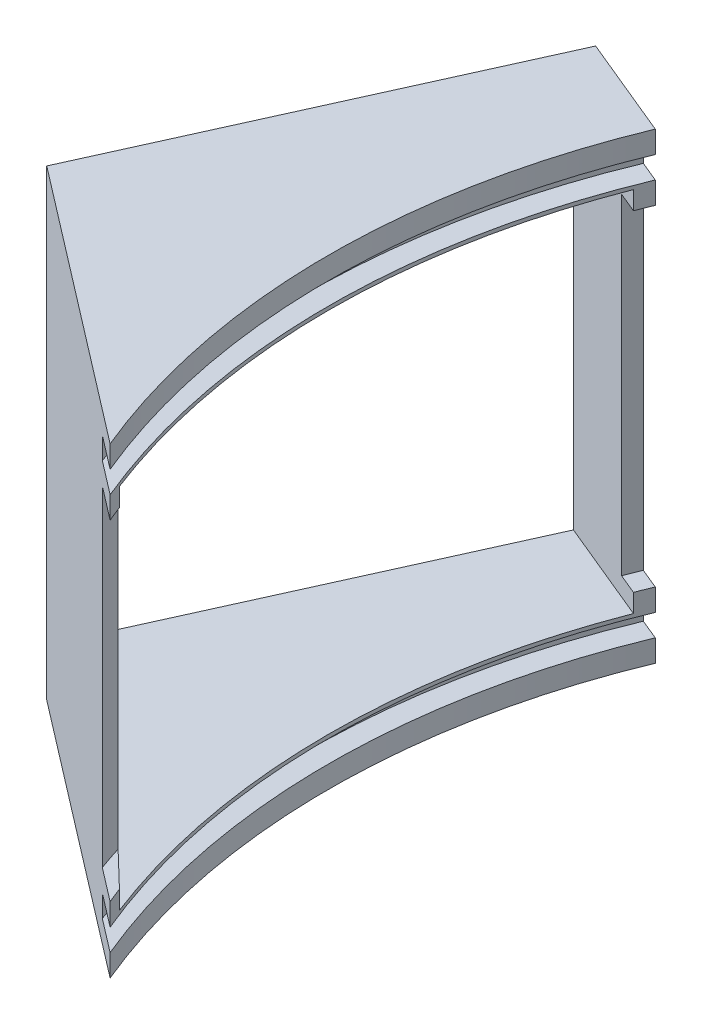
SolidWorks part; units mm, degrees
ref_plane "Front Plane" through (0, 0, 0) normal (0, 0, 1) x (1, 0, 0)
ref_plane "Top Plane" through (0, 0, 0) normal (0, 1, 0) x (1, 0, 0)
ref_plane "Right Plane" through (0, 0, 0) normal (1, 0, 0) x (0, 0, -1)
ref_axis "Axe1" through (0, 55, 0) along (0, -1, 0)
sketch "Esquisse1" plane through (0, 0, 0) normal (0, 0, 1) x (1, 0, 0)
  line L0 (-127, 31.5) -> (-97, 31.5)
  line L1 (-97, 31.5) -> (-97, 28.5)
  line L2 (-97, 28.5) -> (-100, 28.5)
  line L3 (-100, 28.5) -> (-100, 25.5)
  line L4 (-100, 25.5) -> (-97, 25.5)
  line L5 (-97, 25.5) -> (-97, 22.5)
  line L6 (-97, 22.5) -> (-100, 22.5)
  line L7 (-100, 22.5) -> (-100, -22.5)
  line L8 (-100, -22.5) -> (-97, -22.5)
  line L9 (-97, -22.5) -> (-97, -25.5)
  line L10 (-97, -25.5) -> (-100, -25.5)
  line L11 (-100, -25.5) -> (-100, -28.5)
  line L12 (-100, -28.5) -> (-97, -28.5)
  line L13 (-97, -28.5) -> (-97, -31.5)
  line L14 (-97, -31.5) -> (-127, -31.5)
  line L15 (-127, -31.5) -> (-127, 31.5)
  line L16 (0, 55) -> (0, -55) construction
  point P19 (-100, 0)
  dimension "D1" = 45
  dimension "D2" = 97
  dimension "D3" = 3
  dimension "D4" = 3
  dimension "D5" = 3
  dimension "D6" = 30
revolve "Révolution1" add sketch "Esquisse1" angle 45 mid plane about axis through (0, 55, 0) along (0, -1, 0)
sketch "Esquisse3" plane through (0, 0, 0) normal (0, 1, 0) x (1, 0, 0)
  line L0 (-127, 50.1331) -> (-90.4655, 35)
  line L1 (-90.4655, 35) -> (-90.4655, -35)
  line L2 (-90.4655, -35) -> (-127, 0.1331)
  line L3 (-127, 0.1331) -> (-127, 50.1331)
  line L4 (-89.6163, 37.1203) -> (-117.3327, 48.6008) construction
  arc A0 (-117.3327, 48.6008) -> (-117.3327, -48.6008) centre (0, 0) ccw construction
  arc A1 (-89.6163, 37.1203) -> (-89.6163, -37.1203) centre (0, 0) ccw construction
  point P7 (-93.0016, 27.5626)
  point P11 (-92.8992, -27.9058)
  point P12 (-127, 49.4988)
  dimension "D1" = 50
  dimension "D2" = 70
extrude "Enlèv. mat.-Extru.1" cut sketch "Esquisse3" against normal mid plane 50
sketch "Esquisse4" plane through (0, 31.5, 0) normal (0, 1, 0) x (1, 0, 0)
  line L0 (-117.3327, -48.6008) -> (-89.6163, -37.1203)
  line L2 (-126.7043, -8.6617) -> (-89.6163, -37.1203)
  arc A0 (-117.3327, 48.6008) -> (-117.3327, -48.6008) centre (0, 0) ccw construction
  arc A1 (-117.3327, -48.6008) -> (-126.7043, -8.6617) centre (0, 0) cw
  arc A3 (-89.6163, 37.1203) -> (-89.6163, -37.1203) centre (0, 0) ccw construction
  point P2 (0, 0)
  point P3 (0, 0)
  point P4 (-141.8831, 38.4472)
  point P5 (-89.6111, 37.1185)
  point P10 (-142.2599, 37.0286)
  point P11 (-89.6163, 37.1203)
  point P15 (-89.6163, -37.1203)
  point P16 (-117.4928, -48.2124)
  point P17 (0, 0)
  point P18 (-142.143, 37.4749)
  point P21 (-122.8856, -32.0645)
  point P22 (-118.5182, -45.6338)
  point P24 (-122.7008, -32.7646)
  point P25 (-117.3327, -48.6008)
  point P26 (-89.6163, -37.1203)
  point P27 (-122.7008, -32.7646)
  point P28 (0, 0)
  dimension "D1" = 60
extrude "Enlèv. mat.-Extru.2" cut sketch "Esquisse4" against normal through all
sketch "Esquisse5" plane through (0, 31.5, 0) normal (0, 1, 0) x (1, 0, 0)
  line L0 (-126.7043, -8.6617) -> (-148.4614, 8.0331)
  line L1 (-148.4614, 8.0331) -> (-117.3327, 48.6008)
  line L2 (-117.3327, 48.6008) -> (-103.4745, 42.8605)
  line L3 (-89.6163, 37.1203) -> (-117.3327, 48.6008) construction
  line L4 (-103.4745, 42.8605) -> (-126.7043, -8.6617)
  line L5 (-89.6163, -37.1203) -> (-126.7043, -8.6617) construction
  point P10 (-148.5727, 8.1185)
  point P11 (-103.4745, 42.8605)
extrude "Enlèv. mat.-Extru.3" cut sketch "Esquisse5" against normal through all
